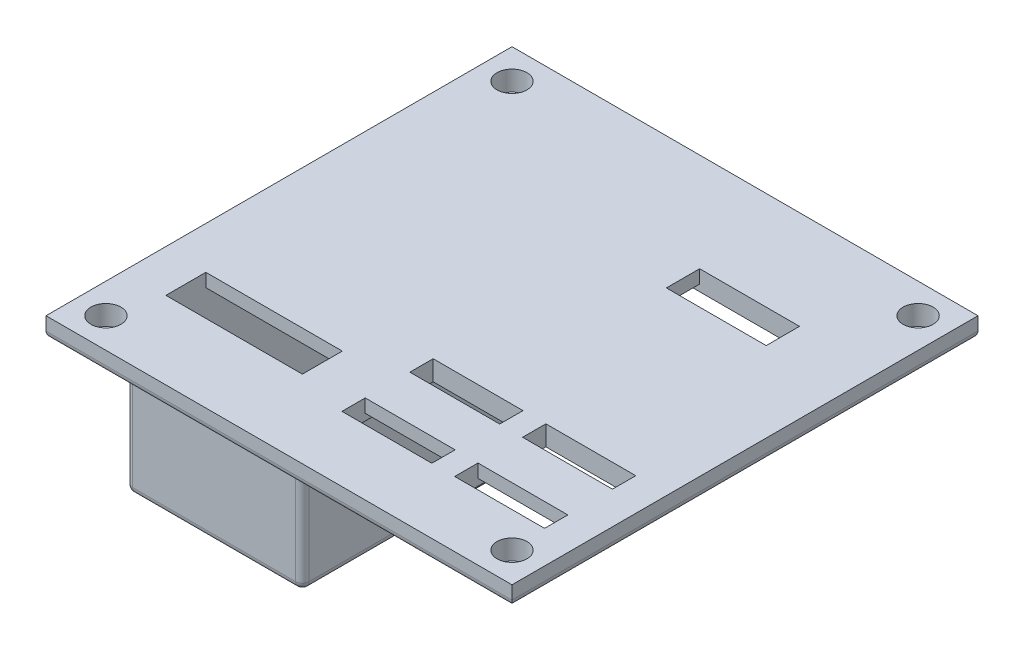
SolidWorks part; units mm, degrees
ref_plane "Front Plane" through (0, 0, 0) normal (0, 0, 1) x (1, 0, 0)
ref_plane "Top Plane" through (0, 0, 0) normal (0, 1, 0) x (1, 0, 0)
ref_plane "Right Plane" through (0, 0, 0) normal (1, 0, 0) x (0, 0, -1)
sketch "Sketch1" plane through (0, 0, 0) normal (0, 1, 0) x (1, 0, 0)
  line L1 (-35, 35) -> (35, 35)
  line L2 (-35, 35) -> (-35, -35)
  line L3 (-35, -35) -> (35, -35)
  line L4 (35, 35) -> (35, -35)
  line L5 (-35, 35) -> (35, -35) construction
  line L6 (-35, -35) -> (35, 35) construction
  point P0 (0, 0)
  dimension "D1" = 70
  dimension "D2" = 70
extrude "Boss-Extrude1" add sketch "Sketch1" along normal blind 3
sketch "Sketch4" plane through (0, 0, 0) normal (0, -1, 0) x (-1, 0, 0)
  line L0 (35, -35) -> (-35, -35) construction
  line L2 (35, 35) -> (35, -35) construction
  circle A0 centre (30.5, -30.5) radius 2.25
  dimension "D1" = 4.5
  dimension "D2" = 4.5
  dimension "D3" = 4.5
extrude "Cut-Extrude2" cut sketch "Sketch4" against normal blind 3
mirror "Mirror1" about plane through (0, 0, 0) normal (1, 0, 0) of "Cut-Extrude2" second plane through (0, 0, 0) second plane normal (0, 0, 1)
fillet "Fillet4" radius 1 4 edges at (0, 0, 35) (-35, 0, 0) (0, 0, -35) (35, 0, 0)
sketch "Sketch5" plane through (0, 0, 0) normal (0, -1, 0) x (-1, 0, 0)
  line L1 (28.7947, -24.7259) -> (7.9947, -24.7259)
  line L2 (28.7947, -24.7259) -> (28.7947, 20.7741)
  line L3 (28.7947, 20.7741) -> (7.9947, 20.7741)
  line L4 (7.9947, -24.7259) -> (7.9947, 20.7741)
  line L5 (28.7947, -24.7259) -> (7.9947, 20.7741) construction
  line L6 (28.7947, 20.7741) -> (7.9947, -24.7259) construction
  point P0 (18.3947, -1.9759)
  point P5 (13.4079, -1.9759)
  point P6 (11.6202, -2.6345)
  point P7 (15.666, -2.4463)
  point P8 (18.3947, -1.9759)
  point P9 (0, 0)
  dimension "D1" = 45.5
  dimension "D2" = 20.8
extrude "Cut-Extrude3" cut sketch "Sketch5" against normal blind 1
sketch "Sketch6" plane through (0, 0, 0) normal (0, -1, 0) x (1, 0, 0)
  line L1 (29.2279, -20.21) -> (1.7279, -20.21)
  line L2 (29.2279, -20.21) -> (29.2279, 7.79)
  line L3 (29.2279, 7.79) -> (1.7279, 7.79)
  line L4 (1.7279, -20.21) -> (1.7279, 7.79)
  line L5 (29.2279, -20.21) -> (1.7279, 7.79) construction
  line L6 (29.2279, 7.79) -> (1.7279, -20.21) construction
  point P0 (15.4779, -6.21)
  point P5 (19.806, -11.5731)
  point P6 (16.7951, -5.8336)
  point P7 (0, 0)
  point P8 (14.7251, -5.4572)
  point P9 (0, 0)
  point P10 (15.1956, -6.5863)
  point P11 (0, 0)
  point P12 (0, 0)
  point P13 (0, 0)
  point P14 (15.2897, -8.5622)
  point P15 (15.1956, -5.8336)
  point P16 (15.4779, -6.21)
  dimension "D1" = 28
  dimension "D2" = 27.5
extrude "Cut-Extrude4" cut sketch "Sketch6" against normal blind 1
sketch "Sketch7" plane through (0, 1, 0) normal (0, -1, 0) x (-1, 0, 0)
  line L0 (-1.7279, 20.21) -> (-29.2279, 20.21) construction
  line L1 (-7.9779, 15.21) -> (-22.9779, 15.21)
  line L2 (-7.9779, 15.21) -> (-7.9779, 20.21)
  line L3 (-7.9779, 20.21) -> (-22.9779, 20.21)
  line L4 (-22.9779, 15.21) -> (-22.9779, 20.21)
  line L5 (-15.4779, -7.79) -> (-15.4779, 20.21) construction
  line L6 (-29.2279, -7.79) -> (-1.7279, -7.79) construction
  line L7 (-1.7279, 20.21) -> (-29.2279, 20.21) construction
  dimension "D1" = 15
  dimension "D2" = 5
  dimension "D3" = 7.5
extrude "Cut-Extrude5" cut sketch "Sketch7" against normal blind 3
sketch "Sketch8" plane through (0, 0, 0) normal (0, -1, 0) x (1, 0, 0)
  line L1 (-0.3293, 25.2162) -> (13.1707, 25.2162)
  line L2 (-0.3293, 25.2162) -> (-0.3293, 11.5162)
  line L3 (-0.3293, 11.5162) -> (13.1707, 11.5162)
  line L4 (13.1707, 25.2162) -> (13.1707, 11.5162)
  line L5 (16.6069, 25.2162) -> (30.1069, 25.2162)
  line L6 (16.6069, 25.2162) -> (16.6069, 11.5162)
  line L7 (16.6069, 11.5162) -> (30.1069, 11.5162)
  line L8 (30.1069, 25.2162) -> (30.1069, 11.5162)
  dimension "D1" = 13.5
  dimension "D2" = 13.7
  dimension "D3" = 13.5
  dimension "D4" = 13.7
extrude "Cut-Extrude6" cut sketch "Sketch8" against normal blind 1
sketch "Sketch9" plane through (0, 1, 0) normal (0, -1, 0) x (-1, 0, 0)
  line L0 (-13.1707, -11.5162) -> (-13.1707, -25.2162) construction
  line L1 (0.3293, -25.2162) -> (-13.1707, -25.2162)
  line L2 (0.3293, -25.2162) -> (0.3293, -21.7162)
  line L3 (0.3293, -21.7162) -> (-13.1707, -21.7162)
  line L4 (-13.1707, -25.2162) -> (-13.1707, -21.7162)
  line L5 (-13.1707, -11.5162) -> (-13.1707, -25.2162) construction
  line L6 (0.3293, -11.5162) -> (-13.1707, -11.5162)
  line L7 (0.3293, -11.5162) -> (0.3293, -15.0162)
  line L8 (0.3293, -15.0162) -> (-13.1707, -15.0162)
  line L9 (-13.1707, -11.5162) -> (-13.1707, -15.0162)
  dimension "D1" = 3.5
  dimension "D2" = 3.5
extrude "Cut-Extrude7" cut sketch "Sketch9" against normal blind 3
sketch "Sketch10" plane through (0, 1, 0) normal (0, -1, 0) x (1, 0, 0)
  line L0 (30.1069, 11.5162) -> (30.1069, 25.2162) construction
  line L1 (16.6069, 25.2162) -> (30.1069, 25.2162)
  line L2 (16.6069, 25.2162) -> (16.6069, 21.7162)
  line L3 (16.6069, 21.7162) -> (30.1069, 21.7162)
  line L4 (30.1069, 25.2162) -> (30.1069, 21.7162)
  line L6 (16.6069, 11.5162) -> (30.1069, 11.5162)
  line L7 (16.6069, 11.5162) -> (16.6069, 15.0162)
  line L8 (16.6069, 15.0162) -> (30.1069, 15.0162)
  line L9 (30.1069, 11.5162) -> (30.1069, 15.0162)
  dimension "D1" = 3.5
  dimension "D2" = 3.5
extrude "Cut-Extrude8" cut sketch "Sketch10" against normal blind 3
sketch "Sketch11" plane through (0, 1, 0) normal (0, -1, 0) x (-1, 0, 0)
  line L0 (7.9947, 20.7741) -> (7.9947, -24.7259) construction
  line L1 (31.6447, -26.3453) -> (5.1447, -26.3453)
  line L2 (31.6447, -26.3453) -> (31.6447, 5.6547)
  line L3 (31.6447, 5.6547) -> (5.1447, 5.6547)
  line L4 (5.1447, -26.3453) -> (5.1447, 5.6547)
  dimension "D1" = 26.5
  dimension "D2" = 32
  dimension "D3" = 2.85
extrude "Boss-Extrude2" add sketch "Sketch11" along normal blind 23.5
sketch "Sketch12" plane through (0, 0, -5.6547) normal (0, 0, -1) x (-1, 0, 0)
  line L0 (-35, 1) -> (35, 1) construction
  line L1 (8.1447, 1) -> (28.6447, 1)
  line L2 (8.1447, 1) -> (8.1447, -19.5)
  line L3 (8.1447, -19.5) -> (28.6447, -19.5)
  line L4 (28.6447, 1) -> (28.6447, -19.5)
  line L5 (31.6447, -22.5) -> (31.6447, 0) construction
  line L6 (5.1447, -22.5) -> (5.1447, 0) construction
  line L7 (31.6447, -22.5) -> (5.1447, -22.5) construction
  dimension "D1" = 3
  dimension "D2" = 3
  dimension "D3" = 3
extrude "Cut-Extrude9" cut sketch "Sketch12" against normal blind 29
sketch "Sketch13" plane through (0, 1, 0) normal (0, -1, 0) x (1, 0, 0)
  line L0 (-8.1447, 23.3453) -> (-8.1447, -5.6547) construction
  line L1 (-28.6447, 23.3453) -> (-8.1447, 23.3453)
  line L2 (-28.6447, 23.3453) -> (-28.6447, 17.3453)
  line L3 (-28.6447, 17.3453) -> (-8.1447, 17.3453)
  line L4 (-8.1447, 23.3453) -> (-8.1447, 17.3453)
  dimension "D1" = 6
extrude "Cut-Extrude10" cut sketch "Sketch13" against normal blind 3
fillet "Fillet5" radius 1 11 edges at (-5.1447, -11.25, 26.3453) (-31.6447, -11.25, 26.3453) (-5.1447, -11.25, -5.6547) (-31.6447, -11.25, -5.6547) (-28.6447, -9.25, -5.6547) (-18.3947, -19.5, -5.6547) (-8.1447, -9.25, -5.6547) (-18.3947, -22.5, 26.3453) (-5.1447, -22.5, 10.3453) (-18.3947, -22.5, -5.6547) (-31.6447, -22.5, 10.3453)
fillet "Fillet6" radius 1 11 edges at (-7.6311, 0, -5.5284) (-6.6447, 0, -5.6547) (-5.4376, 0, -5.3618) (-5.4376, 0, 26.0524) (-31.3518, 0, 26.0524) (-29.1582, 0, -5.5284) (-30.1447, 0, -5.6547) (-31.3518, 0, -5.3618) (-5.1447, 0, 10.3453) (-18.3947, 0, 26.3453) (-31.6447, 0, 10.3453)
sketch "Sketch14" plane through (0, 0, 0) normal (0, -1, 0) x (1, 0, 0)
  line L1 (-28.7947, -20.7741) -> (-7.9947, -20.7741)
  line L2 (-28.7947, -20.7741) -> (-28.7947, -23.7741)
  line L3 (-28.7947, -23.7741) -> (-7.9947, -23.7741)
  line L4 (-7.9947, -20.7741) -> (-7.9947, -23.7741)
  point P5 (-7.9947, -20.7741)
  dimension "D1" = 3
extrude "Cut-Extrude11" cut sketch "Sketch14" against normal blind 1
